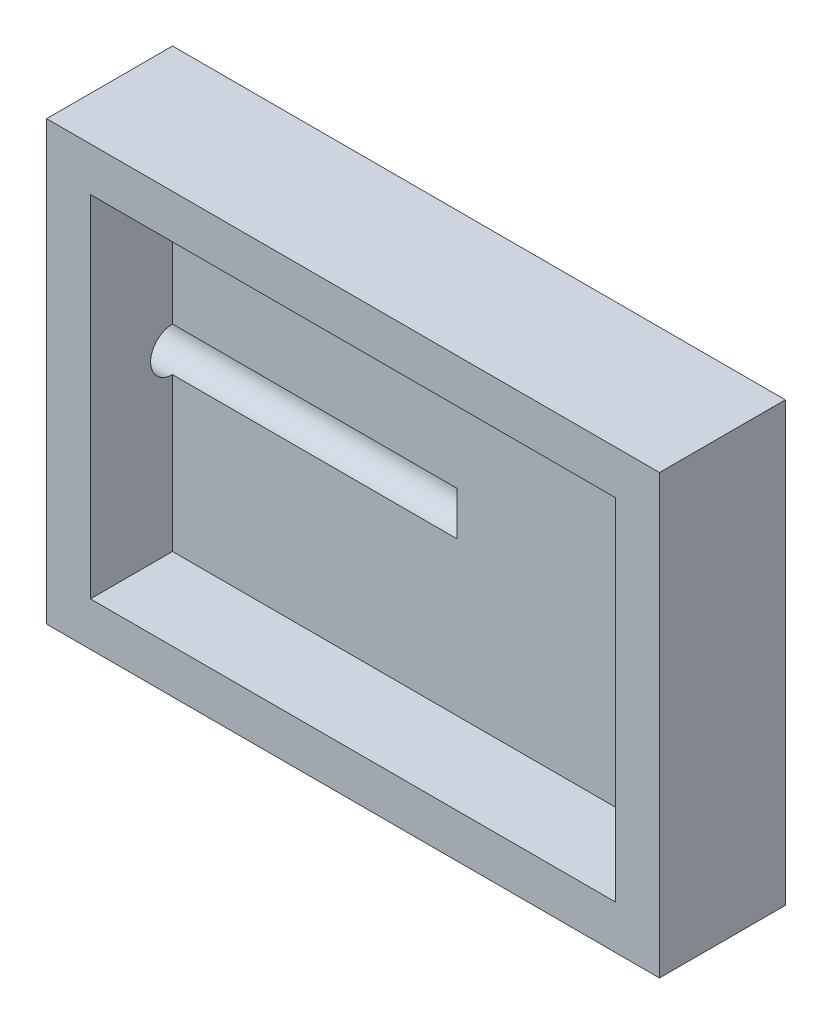
SolidWorks part; units mm, degrees
ref_plane "Front Plane" through (0, 0, 0) normal (0, 0, 1) x (1, 0, 0)
ref_plane "Top Plane" through (0, 0, 0) normal (0, 1, 0) x (1, 0, 0)
ref_plane "Right Plane" through (0, 0, 0) normal (1, 0, 0) x (0, 0, -1)
sketch "Sketch1" plane through (0, 0, 0) normal (0, 0, 1) x (1, 0, 0)
  line L6 (-177.8, -127) -> (177.8, -127)
  line L10 (-177.8, -127) -> (-177.8, 127)
  line L11 (-177.8, 127) -> (177.8, 127)
  line L12 (177.8, -127) -> (177.8, 127)
  line L13 (-177.8, -127) -> (177.8, 127) construction
  line L14 (-177.8, 127) -> (177.8, -127) construction
  point P0 (0, 0)
  dimension "D1" = 355.6
  dimension "D2" = 254
extrude "Boss-Extrude1" add sketch "Sketch1" along normal mid plane 73.025
shell "Shell1" thickness 25.4
sketch "Sketch2" plane through (-177.8, 0, 0) normal (-1, 0, 0) x (0, 0, 1)
  line L0 (-11.1125, 127) -> (-11.1125, -127) construction
  line L1 (36.5125, 127) -> (-36.5125, 127) construction
  line L2 (36.5125, -127) -> (-36.5125, -127) construction
  line L3 (-11.1125, -127) -> (-11.1125, 127) construction
  line L5 (-36.5125, 0) -> (36.5125, 0) construction
  line L6 (-36.5125, 127) -> (-36.5125, -127) construction
  line L7 (36.5125, 127) -> (36.5125, -127) construction
  circle A1 centre (-11.1125, 0) radius 12.7
  dimension "D3" = 25.4
  dimension "D1" = 25.4
  dimension "D2" = 47.625
extrude "Cut-Extrude1" cut sketch "Sketch2" against normal blind 190.5
